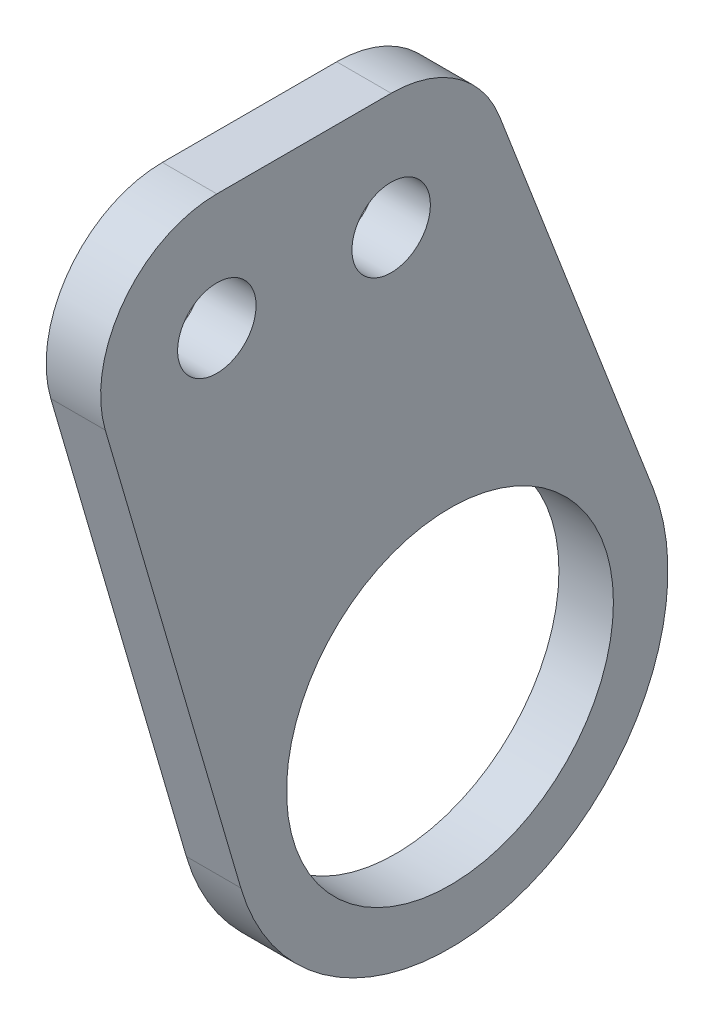
SolidWorks part; units mm, degrees
material "5052-H32"
ref_plane "Front Plane" through (0, 0, 0) normal (0, 0, 1) x (1, 0, 0)
ref_plane "Top Plane" through (0, 0, 0) normal (0, 1, 0) x (1, 0, 0)
ref_plane "Right Plane" through (0, 0, 0) normal (1, 0, 0) x (0, 0, -1)
sketch "Sketch1" plane through (0, 0, 0) normal (1, 0, 0) x (0, 0, -1)
  line L0 (14.2875, 0) -> (14.2875, 38.1) construction
  line L1 (14.2875, 38.1) -> (-20.3835, 38.1) construction
  line L2 (-20.3835, 48.26) -> (-5.1435, 48.26)
  line L3 (-30.1364, 35.2529) -> (-18.2867, -5.3384)
  line L4 (4.338, 41.7507) -> (17.7778, 6.845)
  circle A0 centre (0, 0) radius 14.2875
  circle A1 centre (-20.3835, 38.1) radius 3.429
  circle A2 centre (-5.1435, 38.1) radius 3.429
  arc A3 (-20.3835, 48.26) -> (-30.1364, 35.2529) centre (-20.3835, 38.1) ccw
  arc A4 (4.338, 41.7507) -> (-5.1435, 48.26) centre (-5.1435, 38.1) ccw
  arc A5 (-18.2867, -5.3384) -> (17.7778, 6.845) centre (0, 0) ccw
  dimension "D1" = 28.575
  dimension "D2" = 15.24
  dimension "D3" = 6.858
  dimension "D6" = 10.16
  dimension "D7" = 38.1
  dimension "D4" = 34.671
  dimension "D5" = 38.1
extrude "Boss-Extrude1" add sketch "Sketch1" along normal blind 4.7625
